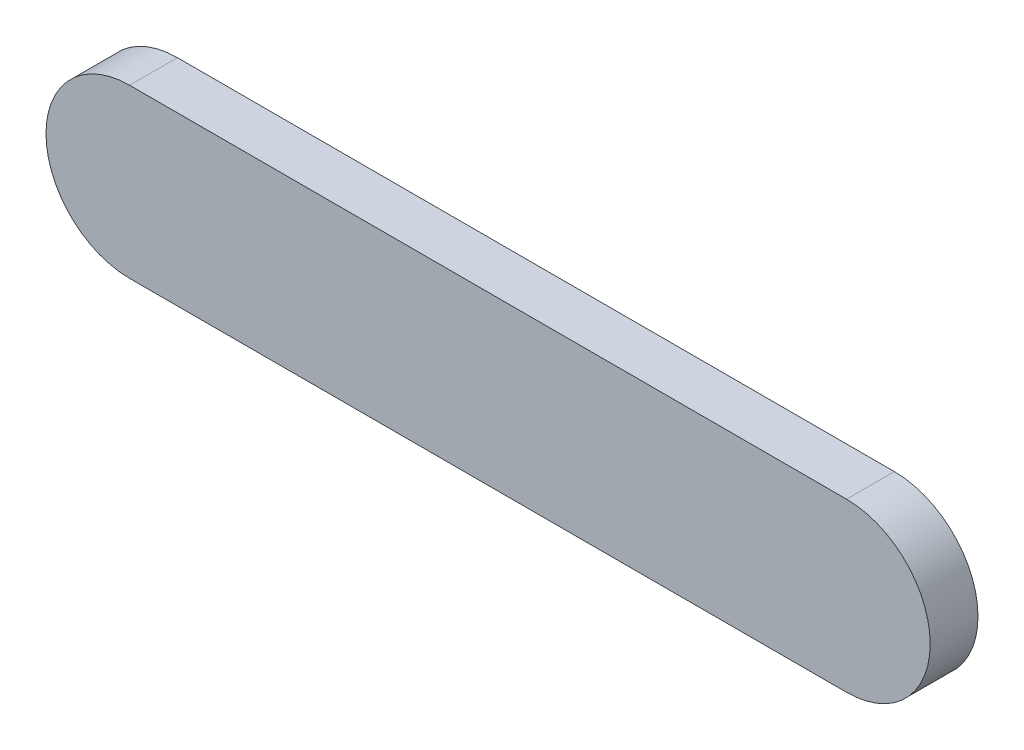
SolidWorks part; units mm, degrees
ref_plane "前视基准面" through (0, 0, 0) normal (0, 0, 1) x (1, 0, 0)
ref_plane "上视基准面" through (0, 0, 0) normal (0, 1, 0) x (1, 0, 0)
ref_plane "右视基准面" through (0, 0, 0) normal (1, 0, 0) x (0, 0, -1)
sketch "草图2" plane through (0, 0, 0) normal (0, 0, 1) x (1, 0, 0)
  line L1 (-90, 21) -> (90, 21)
  line L2 (-90, -21) -> (90, -21)
  arc A0 (-90, 21) -> (-90, -21) centre (-90, 0) ccw
  arc A1 (90, -21) -> (90, 21) centre (90, 0) ccw
  point P4 (0, 0)
  dimension "D2" = 42
  dimension "D1" = 180
extrude "凸台-拉伸1" add sketch "草图2" along normal blind 12
sketch "草图3" plane through (0, 0, 12) normal (0, 0, 1) x (1, 0, 0)
  circle A0 centre (-90, 0) radius 21 construction
sketch "草图1" plane through (0, 0, 0) normal (0, 0, 1) x (1, 0, 0)
  line L1 (-112.5, 21) -> (112.5, 21)
  line L2 (-112.5, -21) -> (112.5, -21)
  arc A0 (-112.5, 21) -> (-112.5, -21) centre (-112.5, 0) ccw
  arc A1 (112.5, -21) -> (112.5, 21) centre (112.5, 0) ccw
  point P4 (0, 0)
  dimension "D2" = 42
  dimension "D1" = 225
